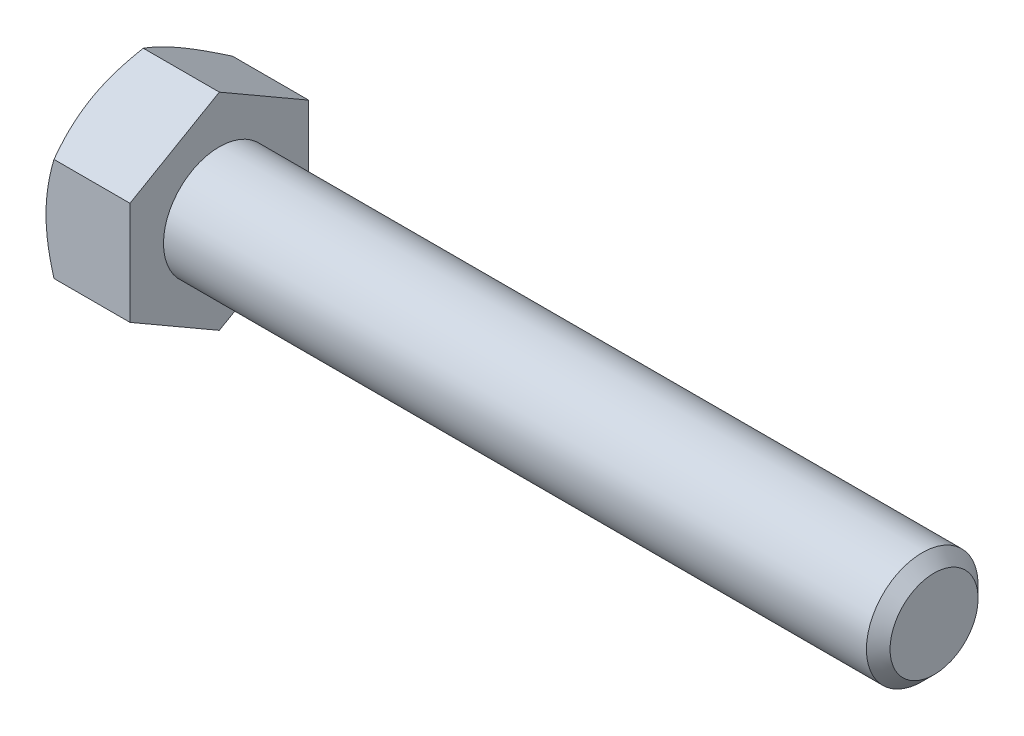
SolidWorks part; units mm, degrees
extrude "BaseHead" add sketch "Sketch1" along normal blind 5.969
sketch "Sketch1" plane through (0, 0, 0) normal (1, 0, 0) x (0, 0, -1)
  line L0 (6.35, 3.6662) -> (6.35, -3.6662)
  line L1 (-6.35, 3.6662) -> (-6.35, -3.6662)
  line L2 (6.35, -3.6662) -> (0, -7.3323)
  line L3 (0, -7.3323) -> (-6.35, -3.6662)
  line L4 (6.35, 3.6662) -> (0, 7.3323)
  line L5 (0, 7.3323) -> (-6.35, 3.6662)
  dimension "Width_flats" = 12.7
  dimension "D2" = 120
  dimension "D3" = 6.35
  dimension "D4" = 6.35
  dimension "D5" = 6.35
ref_plane "Plane1" through (0, 0, 0) normal (0, 0, 1) x (1, 0, 0)
ref_plane "Plane2" through (0, 0, 0) normal (0, 1, 0) x (1, 0, 0)
ref_plane "Plane3" through (0, 0, 0) normal (1, 0, 0) x (0, 0, -1)
sketch "BodySke" plane through (0, 0, 0) normal (0, 0, 1) x (1, 0, 0)
  line L0 (0, 3.6662) -> (0, -3.6662) construction
  line L1 (0, 0) -> (56.769, 0)
  line L2 (0, 0) -> (0, 3.9688)
  line L3 (0, 3.9688) -> (55.9295, 3.9688)
  line L4 (56.769, 0) -> (56.769, 3.1293)
  line L5 (5.969, 7.3323) -> (5.969, 3.6662) construction
  line L6 (56.769, 3.1293) -> (55.9295, 3.9688)
  line L7 (0, 0) -> (96.52, 0) construction
  line L8 (56.769, -3.1293) -> (55.9295, -3.9688) construction
  line L9 (0, -3.9688) -> (55.9295, -3.9688) construction
  line L10 (7.3787, 15.24) -> (7.3787, -2.54) construction
  line L11 (34.544, 15.24) -> (34.544, -2.54) construction
  line L12 (5.969, 3.6662) -> (5.969, -3.6662) construction
  dimension "Diameter" = 7.9375
revolve "BaseBody" add sketch "BodySke" angle 360 about L7
cosmetic thread "ThreadCosmetic" parameters "Thread_length"=22.225, "Thread_minor"=6.2586
sketch "Sketch3" plane through (0, 0, 0) normal (0, 0, 1) x (1, 0, 0)
  line L0 (0, 6.35) -> (4.2333, 13.6823)
  line L1 (0, 7.3323) -> (0, 3.6662) construction
  line L2 (4.2333, 13.6823) -> (4.2333, 20.0323)
  line L3 (4.2333, 20.0323) -> (-12.7, 20.0323)
  line L4 (-12.7, 20.0323) -> (-12.7, 6.35)
  line L5 (-12.7, 6.35) -> (0, 6.35)
  line L6 (0, 0) -> (99.06, 0) construction
  line L7 (5.969, 7.3323) -> (0, 7.3323) construction
  dimension "D4" = 6.35
  dimension "D1" = 6.35
  dimension "D2" = 6.35
  dimension "D3" = 12.7
  dimension "Head_ch_ang" = 30
revolve "HeadChamfer" cut sketch "Sketch3" angle 360 about L6
fillet "HeadFillet" [suppressed] radius 0.762
sketch "ThdSchSke" plane through (0, 0, 0) normal (0, 0, 1) x (1, 0, 0)
  line L0 (34.544, -3.1293) -> (33.9562, -3.9688)
  line L1 (34.544, -3.1293) -> (35.1318, -3.9688)
  line L2 (35.1318, -3.9688) -> (35.1318, -4.9609)
  line L3 (-3.175, 0) -> (5.1513, 0) construction
  line L5 (35.1318, -4.9609) -> (33.9562, -4.9609)
  line L6 (33.9562, -4.9609) -> (33.9562, -3.9688)
  dimension "Thread_minor" = 6.2586
  dimension "Diameter" = 7.9375
  dimension "Start" = 34.544
revolve "ThreadSchematic" [suppressed] cut sketch "ThdSchSke" angle 360 about L3
pattern_linear "ThdSchPat" [suppressed]
equation "\"D3@Sketch1\" = \"Width_flats@Sketch1\" / 2"
equation "\"D4@Sketch1\" = \"D3@Sketch1\""
equation "\"D5@Sketch1\" = \"D4@Sketch1\""
equation "\"Thread_minor@ThreadCosmetic\" = \"Minor_dia@BodySke\""
equation "\"D1@Sketch3\" = \"Width_flats@Sketch1\" / 2"
equation "\"Thread_length@ThreadCosmetic\" = ((sgn( (\"Length@BodySke\" - \"Advance@BodySke\" ) - \"Thread_nom@BodySke\" )-1)*( (\"Length@BodySke\" - \"Advance@BodySke\" ) - \"Thread_nom@BodySke\" ))/-2+ \"Thread_nom@BodySke\""
equation "\"Thread_minor@ThdSchSke\" = \"Minor_dia@BodySke\""
equation "\"Diameter@ThdSchSke\" = \"Diameter@BodySke\""
equation "\"Overcut@ThdSchSke\" = \"Diameter@BodySke\" * 1.25"
equation "\"Start@ThdSchSke\" = \"Head_ht@BaseHead\" + \"Length@BodySke\" - \"Thread_length@ThreadCosmetic\"  '---Non-countersunk---"
equation "\"Num_threads@ThdSchPat\" = int( \"Thread_length@ThreadCosmetic\" / \"Advance@BodySke\" + 0.999 )  + 1"
equation "\"Advance@ThdSchPat\" = \"Thread_length@ThreadCosmetic\" /  (\"Num_threads@ThdSchPat\" - 1) 'relax it"
equation "\"Num_threads@ThdSchPat\" = \"Num_threads@ThdSchPat\" - sgn( \"Num_threads@ThdSchPat\" - 1) '---chamfered tips only---"
